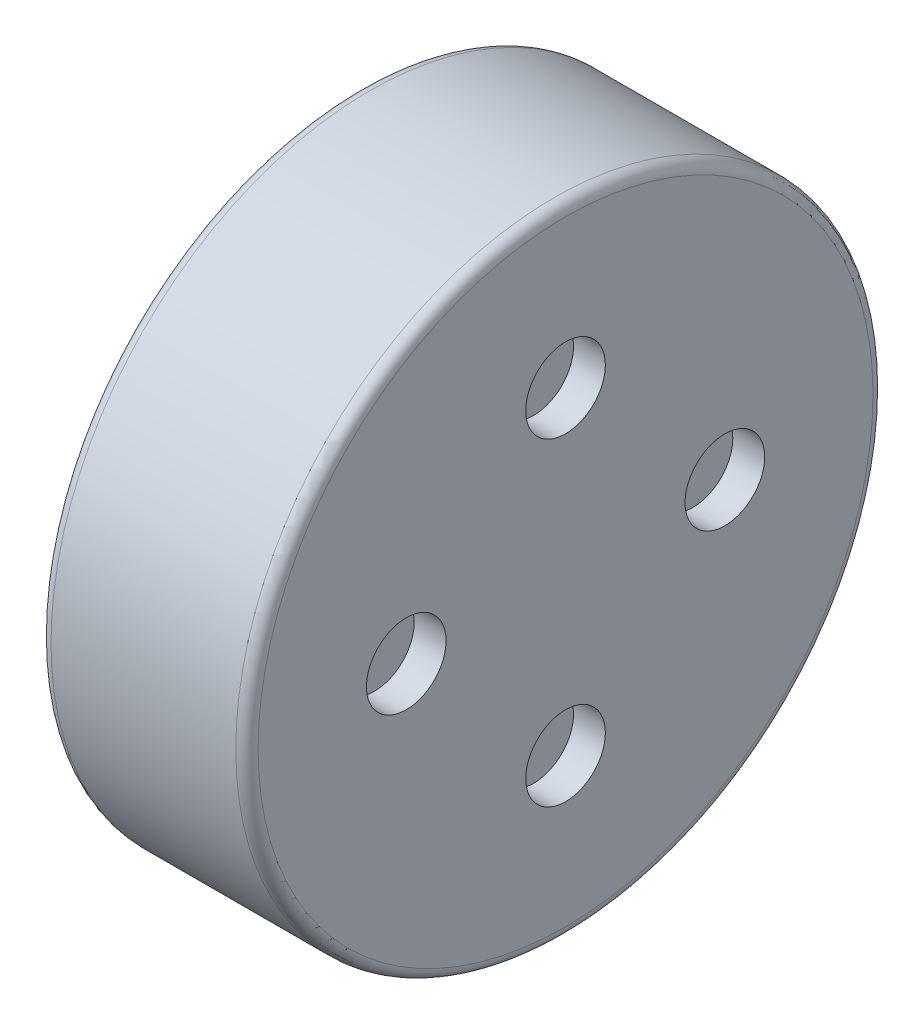
SolidWorks part; units mm, degrees
ref_plane "Front Plane" through (0, 0, 0) normal (0, 0, 1) x (1, 0, 0)
ref_plane "Top Plane" through (0, 0, 0) normal (0, 1, 0) x (1, 0, 0)
ref_plane "Right Plane" through (0, 0, 0) normal (1, 0, 0) x (0, 0, -1)
ref_plane "Plane4" through (0, 0, 0) normal (0, 0, -1) x (-1, 0, 0)
sketch "Sketch1" plane through (0, 0, 0) normal (0, 0, -1) x (-1, 0, 0)
  line L0 (-1.3, 2) -> (-1.3, 0)
  line L1 (-1.3, 0) -> (-0.03, 0)
  line L2 (-0.03, 0) -> (-0.03, 1.8)
  line L3 (-0.03, 1.8) -> (-0.05, 1.8)
  line L4 (0, 1.85) -> (0, 2)
  line L5 (0, 2) -> (-1.3, 2)
  line L6 (-1.3, 0) -> (0, 0) construction
  arc A0 (-0.05, 1.8) -> (0, 1.85) centre (-0.05, 1.85) ccw
revolve "Revolve1" add sketch "Sketch1" angle 360 about L6
sketch "Sketch2" plane through (0.03, 0, 0) normal (-1, 0, 0) x (0, 0, 1)
  circle A0 centre (0, 0) radius 0.9
extrude "Cut-Extrude1" cut sketch "Sketch2" against normal blind 0.05
sketch "Sketch3" plane through (0.08, 0, 0) normal (-1, 0, 0) x (0, 0, 1)
  circle A0 centre (0, 0) radius 0.6
extrude "Boss-Extrude1" add sketch "Sketch3" along normal blind 0.05
sketch "Sketch4" plane through (0.03, 0, 0) normal (-1, 0, 0) x (0, 0, 1)
  circle A0 centre (0, 0) radius 0.275
extrude "Boss-Extrude2" add sketch "Sketch4" along normal blind 0.08
ref_plane "Plane5" through (0, 0, -1.15) normal (0, 0, -1) x (-1, 0, 0)
sketch "Sketch5" plane through (0, 0, -1.15) normal (0, 0, -1) x (-1, 0, 0)
  line L0 (-0.03, 0.2) -> (-0.03, 0)
  line L1 (-0.03, 0) -> (0.05, 0)
  line L2 (0.05, 0) -> (0.05, 0.2)
  line L3 (0.05, 0.2) -> (-0.03, 0.2)
  line L4 (-0.03, 0) -> (0.05, 0) construction
revolve "Revolve2" add sketch "Sketch5" angle 360 about L4
ref_plane "Plane6" through (0, 0, -0.3554) normal (0, 0, -1) x (-1, 0, 0)
sketch "Sketch6" plane through (0, 0, -0.3554) normal (0, 0, -1) x (-1, 0, 0)
  line L0 (-0.03, 1.2937) -> (-0.03, 1.0937)
  line L1 (-0.03, 1.0937) -> (0.05, 1.0937)
  line L2 (0.05, 1.0937) -> (0.05, 1.2937)
  line L3 (0.05, 1.2937) -> (-0.03, 1.2937)
  line L4 (-0.03, 1.0937) -> (0.05, 1.0937) construction
revolve "Revolve3" add sketch "Sketch6" angle 360 about L4
ref_plane "Plane7" through (0, 0, 0.9304) normal (0, 0, -1) x (-1, 0, 0)
sketch "Sketch7" plane through (0, 0, 0.9304) normal (0, 0, -1) x (-1, 0, 0)
  line L0 (-0.03, 0.876) -> (-0.03, 0.676)
  line L1 (-0.03, 0.676) -> (0.05, 0.676)
  line L2 (0.05, 0.676) -> (0.05, 0.876)
  line L3 (0.05, 0.876) -> (-0.03, 0.876)
  line L4 (-0.03, 0.676) -> (0.05, 0.676) construction
revolve "Revolve4" add sketch "Sketch7" angle 360 about L4
sketch "Sketch8" plane through (0, 0, 0.9304) normal (0, 0, -1) x (-1, 0, 0)
  line L0 (-0.03, -0.476) -> (-0.03, -0.676)
  line L1 (-0.03, -0.676) -> (0.05, -0.676)
  line L2 (0.05, -0.676) -> (0.05, -0.476)
  line L3 (0.05, -0.476) -> (-0.03, -0.476)
  line L4 (-0.03, -0.676) -> (0.05, -0.676) construction
revolve "Revolve5" add sketch "Sketch8" angle 360 about L4
sketch "Sketch9" plane through (0, 0, -0.3554) normal (0, 0, -1) x (-1, 0, 0)
  line L0 (-0.03, -0.8937) -> (-0.03, -1.0937)
  line L1 (-0.03, -1.0937) -> (0.05, -1.0937)
  line L2 (0.05, -1.0937) -> (0.05, -0.8937)
  line L3 (0.05, -0.8937) -> (-0.03, -0.8937)
  line L4 (-0.03, -1.0937) -> (0.05, -1.0937) construction
revolve "Revolve6" add sketch "Sketch9" angle 360 about L4
hole_wizard "Hole1" positions "Sketch11" profile "Sketch10" legacy
sketch "Sketch11" plane through (1.3, 0, 0) normal (1, 0, 0) x (0, 0, -1)
  point P0 (-1, 0)
  point P1 (0, -1)
  point P2 (1, 0)
  point P3 (0, 1)
sketch "Sketch10" plane through (1.3, 0, 1) normal (0, 1, 0) x (0, 0, -1)
  line L0 (0, 0) -> (0, 0.2)
  line L1 (0, 0.2) -> (0.25, 0.2)
  line L2 (0.25, 0.2) -> (0.25, 0)
  line L3 (0.25, 0) -> (0, 0)
  line L4 (0, 110) -> (0, -10) construction
  dimension "Diameter" = 0.5
  dimension "Depth" = 0.2
fillet "Fillet1" radius 0.07 8 edges at (-0.05, 0, -0.95) (-0.05, 0.8937, -0.3554) (-0.05, 0.676, 1.1304) (0, 0, 2) (1.3, 0, 2) (-0.05, 0, 0.275) (-0.05, -1.2937, -0.3554) (-0.05, -0.876, 0.9304)
